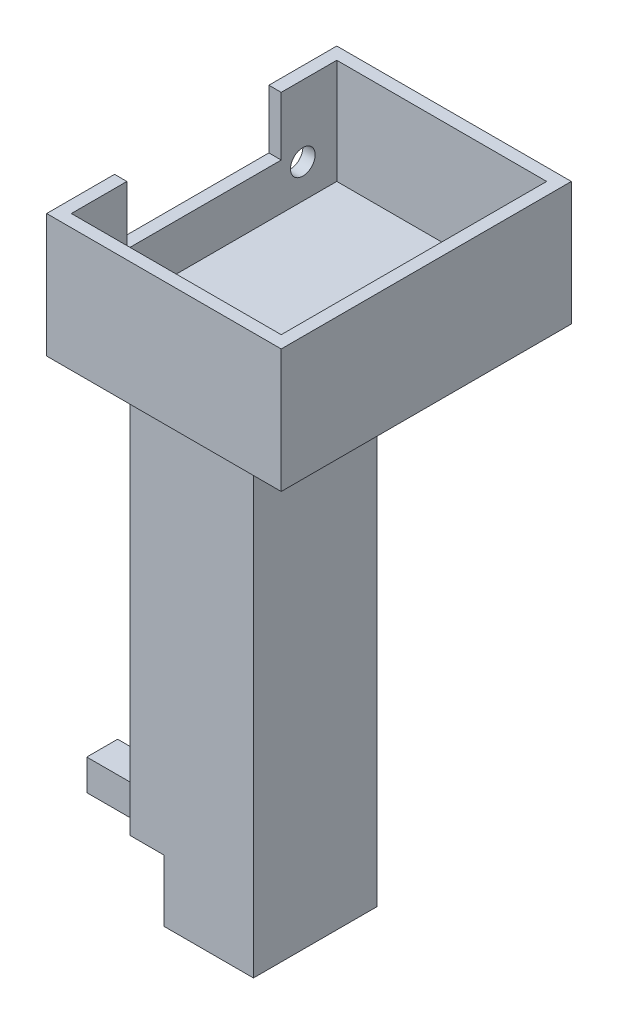
SolidWorks part; units mm, degrees
ref_plane "Front Plane" through (0, 0, 0) normal (0, 0, 1) x (1, 0, 0)
ref_plane "Top Plane" through (0, 0, 0) normal (0, 1, 0) x (1, 0, 0)
ref_plane "Right Plane" through (0, 0, 0) normal (1, 0, 0) x (0, 0, -1)
sketch "Sketch1" plane through (0, 0, 0) normal (0, 1, 0) x (1, 0, 0)
  line L7 (14, 93) -> (48, 93)
  line L8 (14, 93) -> (14, 50)
  line L9 (14, 50) -> (48, 50)
  line L10 (48, 93) -> (48, 50)
  point P4 (11, 96)
  point P5 (11, 47)
  point P6 (51, 47)
  point P8 (0, 0)
  point P10 (7.2222, -2.0222)
  point P12 (21.2222, 47.9778)
  dimension "D1" = 14
  dimension "D2" = 50
  dimension "D3" = 43
  dimension "D4" = 34
sketch "Sketch3" plane through (0, 0, 0) normal (0, 1, 0) x (1, 0, 0)
  line L4 (14, 93) -> (14, 50)
  line L5 (14, 50) -> (48, 50)
  line L6 (48, 50) -> (48, 93)
  line L7 (48, 93) -> (14, 93)
  line L8 (50, 95) -> (12, 95)
  line L9 (50, 48) -> (50, 95)
  line L10 (12, 48) -> (50, 48)
  line L11 (12, 95) -> (12, 48)
  line L12 (50, 95) -> (12, 95)
  line L13 (50, 48) -> (50, 95)
  line L14 (12, 48) -> (50, 48)
  line L15 (12, 95) -> (12, 48)
  dimension "D1" = 2
extrude "Boss-Extrude4" add sketch "Sketch3" along normal blind 10.5
extrude "Boss-Extrude5" add sketch "Sketch1" along normal blind 3
sketch "Sketch7" plane through (0, 10.5, 0) normal (0, 1, 0) x (1, 0, 0)
  line L0 (14, 50) -> (14, 59)
  line L1 (14, 93) -> (14, 50) construction
  line L2 (14, 59) -> (12, 59)
  line L3 (12, 95) -> (12, 48) construction
  line L4 (12, 59) -> (12, 48)
  line L5 (12, 48) -> (50, 48)
  line L6 (50, 48) -> (50, 95)
  line L7 (50, 48) -> (50, 95) construction
  line L8 (48, 93) -> (48, 50)
  line L9 (48, 50) -> (48, 93) construction
  line L10 (48, 50) -> (14, 50)
  line L11 (48, 71.5) -> (50, 71.5) construction
  line L12 (48, 93) -> (14, 93)
  line L13 (12, 95) -> (50, 95)
  line L14 (12, 84) -> (12, 95)
  line L15 (14, 84) -> (12, 84)
  line L16 (14, 93) -> (14, 84)
  dimension "D1" = 9
extrude "Boss-Extrude6" add sketch "Sketch7" along normal blind 9.5
sketch "Sketch6" plane through (14, 0, 0) normal (1, 0, 0) x (0, 0, -1)
  line L0 (50, 3) -> (55.5, 3) construction
  line L1 (93, 3) -> (50, 3) construction
  line L2 (55.5, 3) -> (55.5, 8.5) construction
  line L3 (71.5, 3) -> (71.5, 10.5) construction
  line L4 (84, 10.5) -> (59, 10.5) construction
  circle A0 centre (55.5, 8.5) radius 2
  circle A1 centre (87.5, 8.5) radius 2
  dimension "D3" = 4
  dimension "D1" = 5.5
  dimension "D2" = 5.5
extrude "Cut-Extrude1" cut sketch "Sketch6" against normal up to next
sketch "Sketch8" plane through (0, 0, 0) normal (0, -1, 0) x (1, 0, 0)
  line L0 (12, -95) -> (12, -48) construction
  line L1 (12, -81.5) -> (32, -81.5)
  line L2 (12, -81.5) -> (12, -61.5)
  line L3 (12, -61.5) -> (32, -61.5)
  line L4 (32, -81.5) -> (32, -61.5)
  line L5 (32, -71.5) -> (50, -71.5) construction
  line L6 (50, -48) -> (50, -95) construction
  dimension "D1" = 20
  dimension "D2" = 20
extrude "Boss-Extrude7" add sketch "Sketch8" along normal offset from surface (84 mm away) 87 up to face at (31, 3, -71.5)
sketch "Sketch11" plane through (12, 0, 0) normal (-1, 0, 0) x (0, 0, 1)
  line L0 (-74, -74) -> (-81.5, -74)
  line L1 (-81.5, -84) -> (-81.5, 0) construction
  line L2 (-81.5, -74) -> (-81.5, -84)
  line L3 (-81.5, -84) -> (-61.5, -84)
  line L4 (-61.5, -84) -> (-61.5, -74)
  line L5 (-61.5, -84) -> (-61.5, 0) construction
  line L6 (-61.5, -74) -> (-69, -74)
  line L7 (-69, -74) -> (-69, -79)
  line L8 (-69, -79) -> (-74, -79)
  line L9 (-74, -79) -> (-74, -74)
  line L10 (-74, -74) -> (-69, -74) construction
  dimension "D1" = 10
  dimension "D2" = 5
extrude "Cut-Extrude2" cut sketch "Sketch11" against normal blind 5.5
sketch "Sketch12" plane through (12, 0, 0) normal (-1, 0, 0) x (0, 0, 1)
  line L1 (-74, -79) -> (-69, -79)
  line L2 (-74, -79) -> (-74, -74)
  line L3 (-74, -74) -> (-69, -74)
  line L4 (-69, -79) -> (-69, -74)
extrude "Boss-Extrude11" add sketch "Sketch12" along normal offset from surface (14.5 mm away) 20 up to face at (17.5, -77.75, -71.5) offset beyond the face yes
